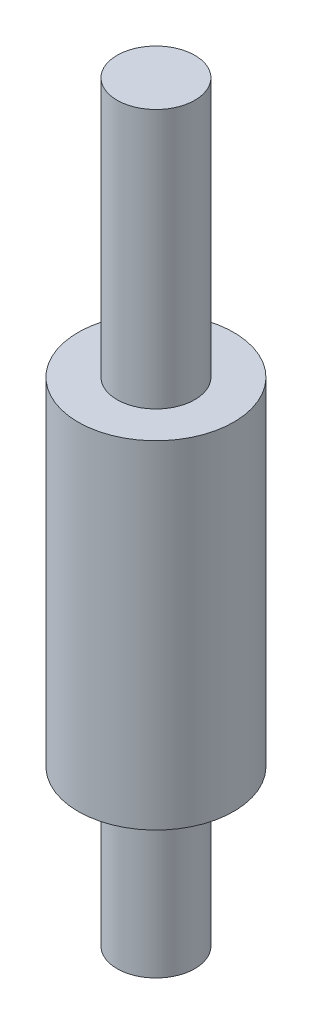
SolidWorks part; units mm, degrees
ref_plane "Front Plane" through (0, 0, 0) normal (0, 0, 1) x (1, 0, 0)
ref_plane "Top Plane" through (0, 0, 0) normal (0, 1, 0) x (1, 0, 0)
ref_plane "Right Plane" through (0, 0, 0) normal (1, 0, 0) x (0, 0, -1)
sketch "Sketch1" plane through (0, 0, 0) normal (0, 1, 0) x (1, 0, 0)
  circle A0 centre (0, 0) radius 1.5
  dimension "D1" = 3
extrude "Boss-Extrude1" add sketch "Sketch1" along normal blind 6
cosmetic thread "Cosmetic Thread2" parameters "D2"=2.439
sketch "Sketch2" plane through (0, 6, 0) normal (0, 1, 0) x (1, 0, 0)
  circle A0 centre (0, 0) radius 3
  dimension "D1" = 6
extrude "Boss-Extrude2" add sketch "Sketch2" along normal blind 13
sketch "Sketch3" plane through (0, 19, 0) normal (0, 1, 0) x (1, 0, 0)
  circle A0 centre (0, 0) radius 1.5
  dimension "D1" = 3
extrude "Boss-Extrude3" add sketch "Sketch3" along normal blind 10
cosmetic thread "Cosmetic Thread1" parameters "D2"=2.439
